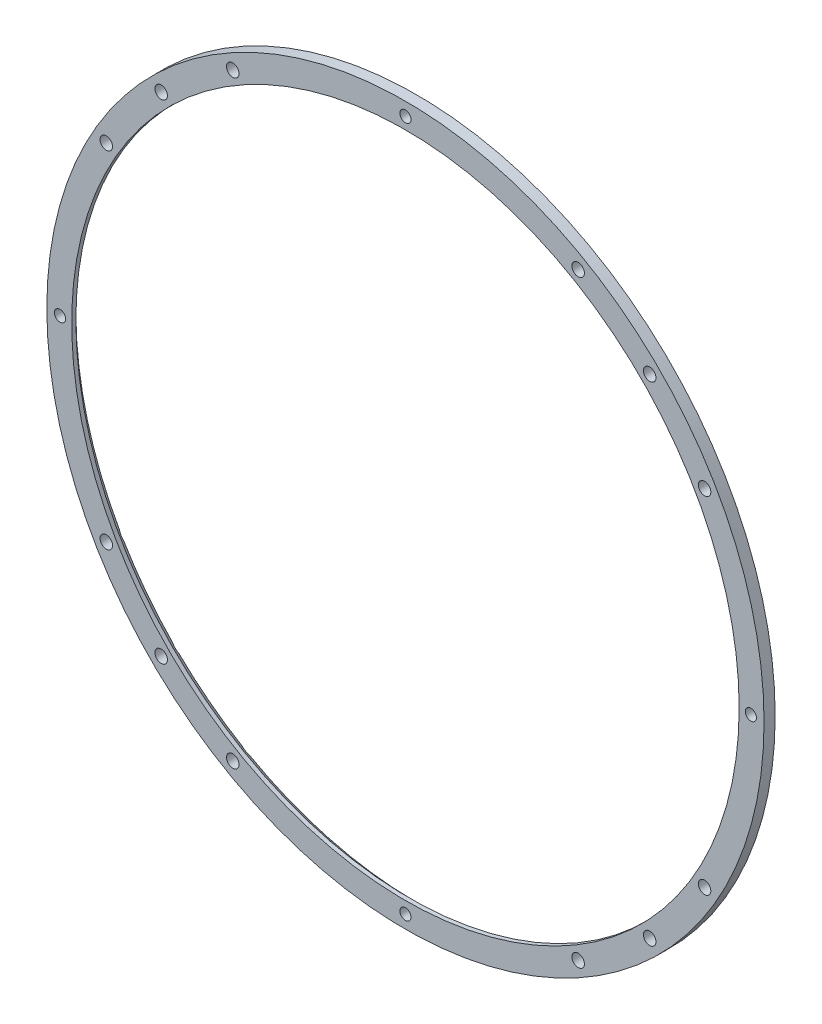
SolidWorks part; units mm, degrees
material "Thornel Mat VMA"
ref_plane "Front" through (0, 0, 0) normal (0, 0, 1) x (1, 0, 0)
ref_plane "Top" through (0, 0, 0) normal (0, 1, 0) x (1, 0, 0)
ref_plane "Right" through (0, 0, 0) normal (1, 0, 0) x (0, 0, -1)
sketch "Sketch1" plane through (0, 0, 0) normal (1, 0, 0) x (0, 0, -1)
  line L0 (-27.3494, 0) -> (20.9856, 0) construction
  line L1 (0, 0) -> (0, 58.9414) construction
  line L2 (0, 122.55) -> (-2.5, 120.05)
  line L3 (0, 129) -> (-4, 129)
  line L4 (0, 129) -> (0, 122.55)
  line L5 (-2.5, 120.05) -> (-4, 120.05)
  line L6 (-4, 129) -> (-4, 120.05)
  point P7 (0, 120.05)
  dimension "D1" = 129
  dimension "D2" = 4
  dimension "D4" = 240.1
revolve "Revolve1" add sketch "Sketch1" angle 360 about L0
hole_wizard "Ø4.5 (4.5) Diameter Hole1" positions "Sketch3" profile "Sketch2" hole size "Ø4.5" standard "Ansi Metric" end condition through all
sketch "Sketch3" plane through (0, 0, 4) normal (0, 0, 1) x (1, 0, 0)
  line L0 (62.125, 107.6037) -> (0, 0)
  line L2 (0, 0) -> (0, 41.1264) construction
  point P0 (62.125, 107.6037)
  dimension "D1" = 124.25
  dimension "D2" = 30
sketch "Sketch2" plane through (62.125, 107.6037, 4) normal (1, 0, 0) x (0, -1, 0)
  line L0 (0, 0) -> (0, 4)
  line L1 (0, 4) -> (2.25, 4)
  line L2 (2.25, 4) -> (2.25, 0)
  line L5 (2.25, 0) -> (0, 0)
  line L11 (0, -6.35) -> (0, 107.95) construction
  dimension "Thru Hole Dia." = 4.5
  dimension "Thru Hole Depth" = 4
ref_axis "Axis1" through (0, 0, -80.9) along (0, 0, 1)
pattern_circular "CirPattern1" count 12 over 360 about axis through (0, 0, -80.9) along (0, 0, 1) skipping 1, 4, 7, 10 of "Ø4.5 (4.5) Diameter Hole1"
hole_wizard "Ø4.0 (4) Diameter Hole1" positions "Sketch5" profile "Sketch4" hole size "Ø4.0" standard "Ansi Metric" end condition through all
sketch "Sketch5" plane through (0, 0, 4) normal (0, 0, 1) x (1, 0, 0)
  line L0 (107.6037, 62.125) -> (0, 0)
  line L2 (0, 0) -> (124.25, 0)
  point P1 (124.25, 0)
sketch "Sketch4" plane through (124.25, 0, 4) normal (1, 0, 0) x (0, -1, 0)
  line L0 (0, 0) -> (0, 4.1141)
  line L1 (0, 4.1141) -> (2, 4.1141)
  line L2 (2, 4.1141) -> (2, 0)
  line L5 (2, 0) -> (0, 0)
  line L11 (0, -6.35) -> (0, 107.95) construction
  dimension "Thru Hole Dia." = 4
  dimension "Thru Hole Depth" = 4.1141
pattern_circular "CirPattern2" count 4 over 360 about axis through (0, 0, 0) along (0, 0, 1) of "Ø4.0 (4) Diameter Hole1"
hole_wizard "Ø4.5 (4.5) Diameter Hole2" positions "Sketch7" profile "Sketch6" hole size "Ø4.5" standard "Ansi Metric" end condition through all
sketch "Sketch7" plane through (0, 0, 4) normal (0, 0, 1) x (1, 0, 0)
  line L0 (0, 124.25) -> (0, 0)
  line L1 (0, 0) -> (87.858, 87.858)
  point P0 (87.858, 87.858)
  dimension "D1" = 45
sketch "Sketch6" plane through (87.858, 87.858, 4) normal (1, 0, 0) x (0, -1, 0)
  line L0 (0, 0) -> (0, 4.1141)
  line L1 (0, 4.1141) -> (2.25, 4.1141)
  line L2 (2.25, 4.1141) -> (2.25, 0)
  line L5 (2.25, 0) -> (0, 0)
  line L11 (0, -6.35) -> (0, 107.95) construction
  dimension "Thru Hole Dia." = 4.5
  dimension "Thru Hole Depth" = 4.1141
pattern_circular "CirPattern3" count 4 over 360 about axis through (0, 0, 0) along (0, 0, 1) of "Ø4.5 (4.5) Diameter Hole2"
